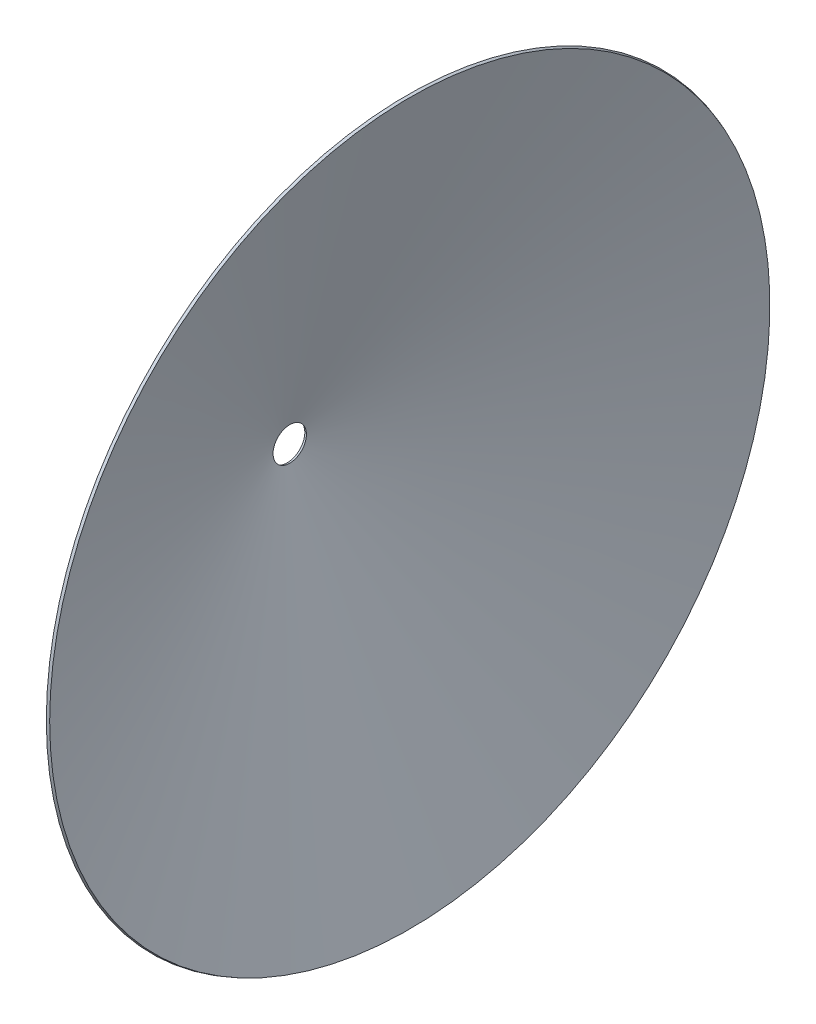
SolidWorks part; units mm, degrees
material "Acrylic (Medium-high impact)"
ref_plane "Front Plane" through (0, 0, 0) normal (0, 0, 1) x (1, 0, 0)
ref_plane "Top Plane" through (0, 0, 0) normal (0, 1, 0) x (1, 0, 0)
ref_plane "Right Plane" through (0, 0, 0) normal (1, 0, 0) x (0, 0, -1)
sketch "Sketch1" plane through (0, 0, 0) normal (0, 1, 0) x (1, 0, 0)
  line L0 (0, 312.4162) -> (457.2, 312.4162) construction
  line L1 (0, 248.9162) -> (457.2, -1059.1838)
  point P2 (0, 0)
  dimension "D1" = 457.2
  dimension "D2" = 1371.6
  dimension "D3" = 63.5
revolve "Revolve-Thin1" add sketch "Sketch1" angle 360 about L0
